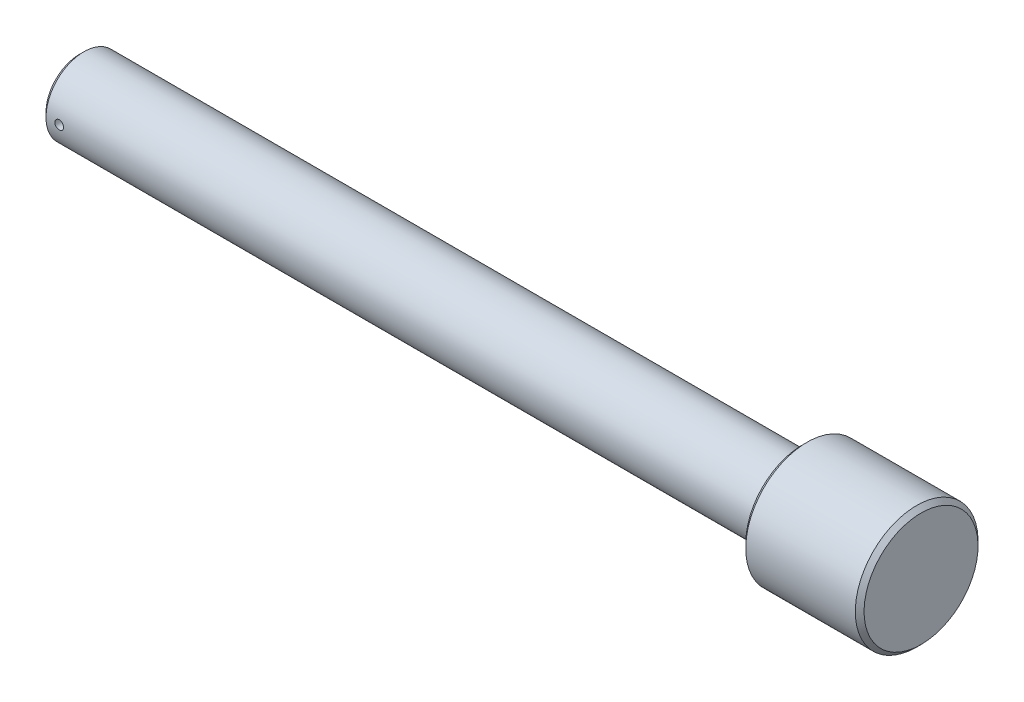
SolidWorks part; units mm, degrees
ref_plane "Plan de face" through (0, 0, 0) normal (0, 0, 1) x (1, 0, 0)
ref_plane "Plan de dessus" through (0, 0, 0) normal (0, 1, 0) x (1, 0, 0)
ref_plane "Plan de droite" through (0, 0, 0) normal (1, 0, 0) x (0, 0, -1)
sketch "Esquisse1" plane through (0, 0, 0) normal (0, 0, 1) x (1, 0, 0)
  line L0 (0, 0) -> (192, 0) construction
  line L1 (0, 0) -> (0, 7.65)
  line L2 (1, 8.65) -> (165, 8.65)
  line L3 (165, 8.65) -> (165, 13)
  line L4 (166, 14) -> (191, 14)
  line L5 (192, 13) -> (192, 0)
  line L6 (0, 7.65) -> (1, 8.65)
  line L7 (165, 13) -> (166, 14)
  line L8 (191, 14) -> (192, 13)
  line L9 (0, 0) -> (192, 0)
  point P4 (0, 8.65)
  point P6 (165, 14)
  point P7 (192, 14)
  dimension "D1" = 165
  dimension "D2" = 17.3
  dimension "D3" = 28
  dimension "D4" = 25
revolve "Révolution1" add sketch "Esquisse1" angle 360 about L0
sketch "Esquisse2" plane through (0, 0, 0) normal (0, 0, 1) x (1, 0, 0)
  circle A0 centre (4, 0) radius 1
  dimension "D1" = 2
  dimension "D2" = 4
extrude "Enlèv. mat.-Extru.1" cut sketch "Esquisse2" against normal through all and the other way through all
